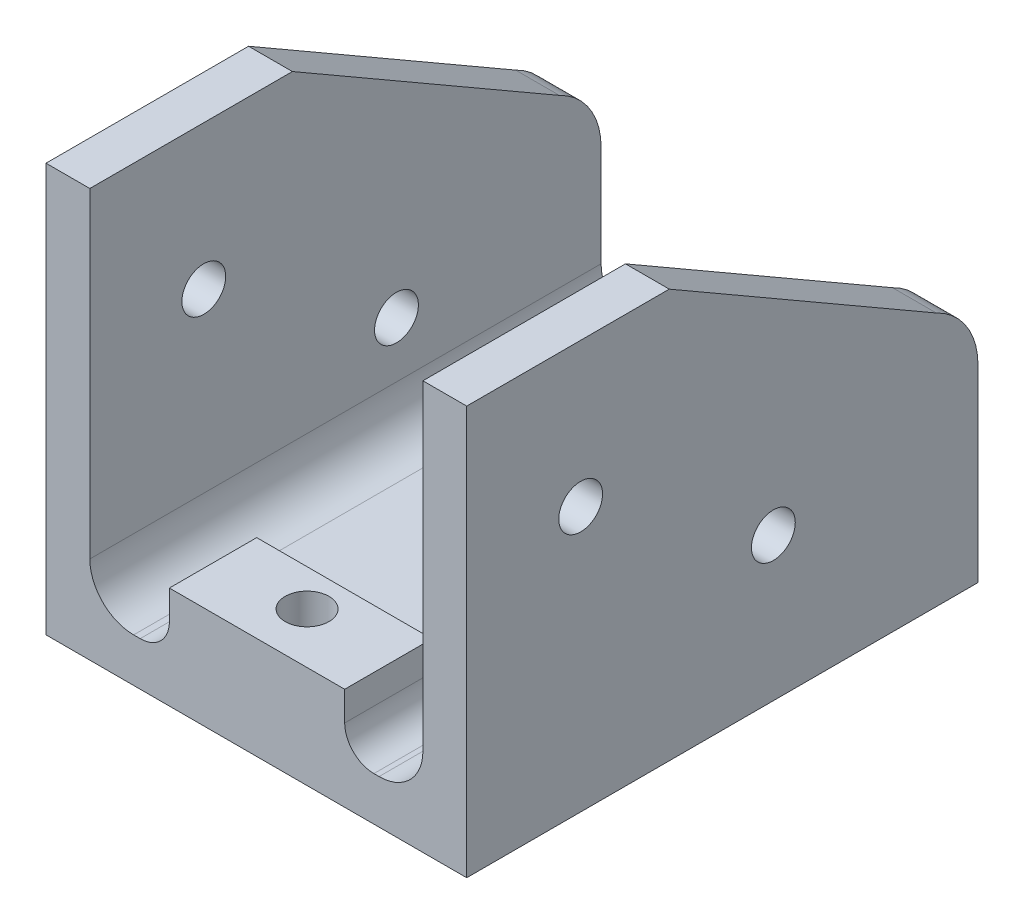
SolidWorks part; units mm, degrees
ref_plane "前视基准面" through (0, 0, 0) normal (0, 0, 1) x (1, 0, 0)
ref_plane "上视基准面" through (0, 0, 0) normal (0, 1, 0) x (1, 0, 0)
ref_plane "右视基准面" through (0, 0, 0) normal (1, 0, 0) x (0, 0, -1)
sketch "草图1" plane through (0, 0, 0) normal (0, 0, 1) x (1, 0, 0)
  line L0 (-25.8, 21.6618) -> (-25.8, -6.2453)
  line L1 (-25.8, -6.2453) -> (3, -6.2453)
  line L2 (3, -6.2453) -> (3, 21.7182)
  line L3 (3, 21.7182) -> (0, 21.7182)
  line L4 (0, 21.7182) -> (0, -3.2453)
  line L5 (0, -3.2453) -> (-22.8, -3.2453)
  line L6 (-22.8, -3.2453) -> (-22.8, 21.7182)
  line L7 (-22.8, 21.7182) -> (-25.8, 21.7182)
  line L8 (-25.8, 21.7182) -> (-25.8, 21.6618)
  dimension "D1" = 22.8
  dimension "D2" = 28.8
  dimension "D3" = 3
  dimension "D4" = 3
  dimension "D5" = 3
extrude "凸台-拉伸1" add sketch "草图1" along normal blind 35
sketch "草图7" plane through (0, -3.2453, 0) normal (0, 1, 0) x (1, 0, 0)
  line L0 (-5.4, -6.5226) -> (-17.4, -6.5226)
  line L2 (-17.4, -6.5226) -> (-17.4, -0.0226)
  line L3 (-17.4, -0.0226) -> (-5.4, -0.0226)
  line L4 (-5.4, -6.5226) -> (-5.4, -0.0226)
  line L6 (-22.8, -35) -> (-22.8, 0) construction
  dimension "D1" = 12
  dimension "D2" = 5.4
extrude "凸台-拉伸3" add sketch "草图7" along normal blind 4
sketch "草图2" plane through (0, -3.2453, 0) normal (0, 1, 0) x (1, 0, 0)
  line L0 (-22.8, -17.5) -> (-14.65, -17.5) construction
  line L1 (-17.4, -1.5) -> (-5.4, -1.5) construction
  line L2 (-17.4, -1.5) -> (-17.4, -33.5) construction
  line L3 (-17.4, -33.5) -> (-5.4, -33.5) construction
  line L4 (-5.4, -1.5) -> (-5.4, -33.5) construction
  line L5 (-17.4, -1.5) -> (-11.4, -17.5) construction
  line L6 (-17.4, -33.5) -> (-5.4, -1.5) construction
  line L7 (-13.7452, -17.5) -> (-11.4, -17.5) construction
  line L8 (-22.8, -35) -> (-22.8, 0) construction
  line L9 (-11.4, -17.5) -> (-11.4, -35) construction
  line L10 (0, -35) -> (-22.8, -35) construction
  line L11 (-11.4, -6.5) -> (-11.4, -18) construction
  line L12 (-14.8459, -6.5) -> (-7.9541, -6.5) construction
  line L13 (-14.8459, -6.5) -> (-14.8459, -28.5) construction
  line L14 (-14.8459, -28.5) -> (-7.9541, -28.5) construction
  line L15 (-7.9541, -6.5) -> (-7.9541, -28.5) construction
  line L16 (-14.8459, -6.5) -> (-11.4, -17.5) construction
  line L17 (-14.8459, -28.5) -> (-7.9541, -6.5) construction
  line L18 (-14.65, -18) -> (-14.65, -16.9934)
  line L19 (-8.15, -18) -> (-8.15, -16.9934)
  line L20 (-11.244, -17.9979) -> (-7.9541, -28.5) construction
  line L21 (-11.2136, -17.997) -> (-5.4, -33.5) construction
  line L22 (-11.4, -6.5) -> (-11.4, -4.3296) construction
  line L23 (-11.4, -4.3296) -> (-11.4, -31.5296) construction
  arc A1 (-14.65, -18) -> (-8.15, -18) centre (-11.4, -18) ccw
  arc A2 (-8.15, -16.9934) -> (-14.65, -16.9934) centre (-11.4, -12.25) ccw
  arc A3 (-10.4249, -14.8997) -> (-10.5721, -14.8572) centre (-11.4, -18) ccw construction
  arc A4 (-12.2279, -14.8572) -> (-12.3751, -14.8997) centre (-11.4, -18) ccw construction
  circle A5 centre (-11.4, -4.3296) radius 1.5
  circle A6 centre (-11.4, -31.5296) radius 1.5
  point P0 (-11.4, -17.5)
  dimension "D5" = 6.5
  dimension "D6" = 3
  dimension "D8" = 3
  dimension "D1" = 12
  dimension "D2" = 32
  dimension "D3" = 22
  dimension "D4" = 11.5
  dimension "D7" = 27.2
extrude "切除-拉伸1" cut sketch "草图2" against normal up to next
sketch "草图5" plane through (-25.8, 0, 0) normal (-1, 0, 0) x (0, 0, 1)
  line L0 (0, 6.6472) -> (0, 21.7182)
  line L1 (0, 21.7182) -> (0, -6.2453) construction
  line L2 (0, 21.7182) -> (21.134, 21.7182)
  line L3 (35, 21.7182) -> (0, 21.7182) construction
  line L4 (19.6104, 20.8386) -> (109.677, 72.8386) construction
  line L5 (21.134, 21.7182) -> (2.8434, 11.1581)
  arc A0 (2.8434, 11.1581) -> (0, 6.6472) centre (5, 6.6472) ccw construction
  arc A1 (2.8434, 11.1581) -> (0, 6.6472) centre (5, 6.6472) ccw
extrude "切除-拉伸2" cut sketch "草图5" against normal up to surface (28.8 mm away) up to face at (3, 7.7365, 17.5)
sketch "草图6" plane through (0, -3.2453, 0) normal (0, 1, 0) x (1, 0, 0)
  line L7 (0, -35) -> (-22.8, -35) construction
  line L8 (-5.3537, -35) -> (-17.3537, -35)
  line L9 (-17.3537, -35) -> (-17.3537, -29.0226)
  line L10 (-17.3537, -29.0226) -> (-5.3537, -29.0226)
  line L11 (-5.3537, -29.0226) -> (-5.3537, -35)
  line L20 (-10.8904, -6.5226) -> (-5.4, -6.5226) construction
  circle M6 centre (-11.4, -31.5296) radius 1.5
  line M14 (-22.8, -35) -> (0, -35)
  dimension "D1" = 22.5
  dimension "D2" = 12
extrude "凸台-拉伸2" add sketch "草图6" along normal blind 4 contours L11 L10 L9 M14 M6
sketch "草图9" plane through (0, -6.2453, 0) normal (0, -1, 0) x (1, 0, 0)
  circle A0 centre (-11.4, 4.3296) radius 1.5
extrude "切除-拉伸3" cut sketch "草图9" against normal up to next
fillet "圆角1" radius 3 2 edges at (0, -3.2453, 17.5) (-22.8, -3.2453, 17.5)
fillet "圆角2" radius 2 4 edges at (-17.3537, -3.2453, 32.0113) (-17.4, -3.2453, 3.2726) (-5.4, -3.2453, 3.2726) (-5.3537, -3.2453, 32.0113)
hole_wizard "大小mm Clearance 暗销孔1" positions "草图10" profile "草图11" hole size "Ø3.0" standard "ISO" end condition through all
sketch "草图10" plane through (3, -125.3152, 113.1074) normal (1, 0, 0) x (0, 0.0223, -0.9998)
  point P0 (88.939, 135.2274)
  point P2 (101.9425, 126.6475)
  point P4 (127.5376, 125.5988)
  point P7 (135.4543, 124.4474)
sketch "草图11" plane through (3, 11.8579, 27.1997) normal (0, 1, 0) x (0, 0, -1)
  line L0 (0, 0) -> (0, 28.8)
  line L1 (0, 28.8) -> (1.5, 28.8)
  line L2 (1.5, 28.8) -> (1.5, 0)
  line L3 (1.5, 0) -> (0, 0)
  line L4 (0, -6.35) -> (0, 107.95) construction
  dimension "通孔孔直径" = 3
  dimension "通孔孔深度" = 28.8
